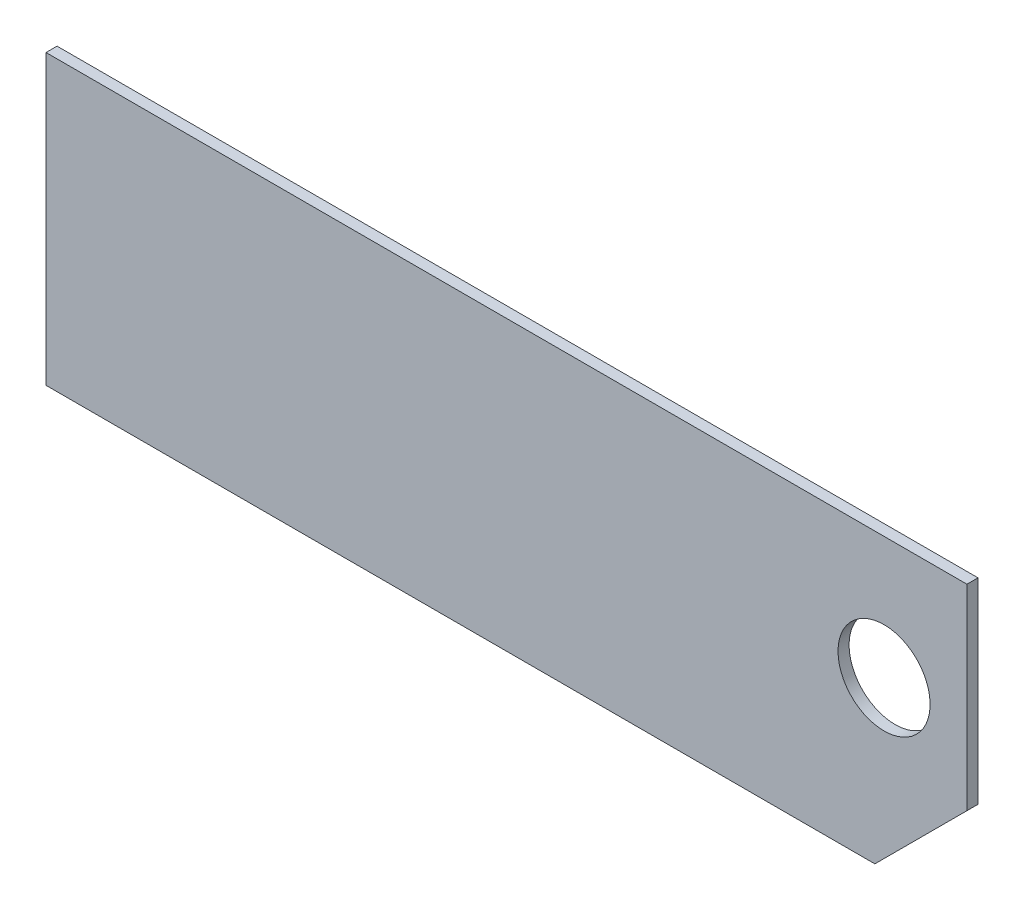
SolidWorks part; units mm, degrees
ref_plane "Front Plane" through (0, 0, 0) normal (0, 0, 1) x (1, 0, 0)
ref_plane "Top Plane" through (0, 0, 0) normal (0, 1, 0) x (1, 0, 0)
ref_plane "Right Plane" through (0, 0, 0) normal (1, 0, 0) x (0, 0, -1)
ref_plane "Plane1" through (0, 0, 6) normal (0, 0, 1) x (1, 0, 0)
sketch "Sketch1" plane through (0, 0, 6) normal (0, 0, 1) x (1, 0, 0)
  line L0 (-200, -90) -> (250, -90)
  line L1 (250, -90) -> (300, -40)
  line L2 (300, -40) -> (300, 66.5)
  line L3 (300, 66.5) -> (-200, 66.5)
  line L4 (-200, 66.5) -> (-200, -90)
  circle A0 centre (255, 0) radius 25
extrude "Boss-Extrude1" add sketch "Sketch1" against normal blind 6
scale "Scale1" scale about centroid uniform scaling yes scale factor 0.75
